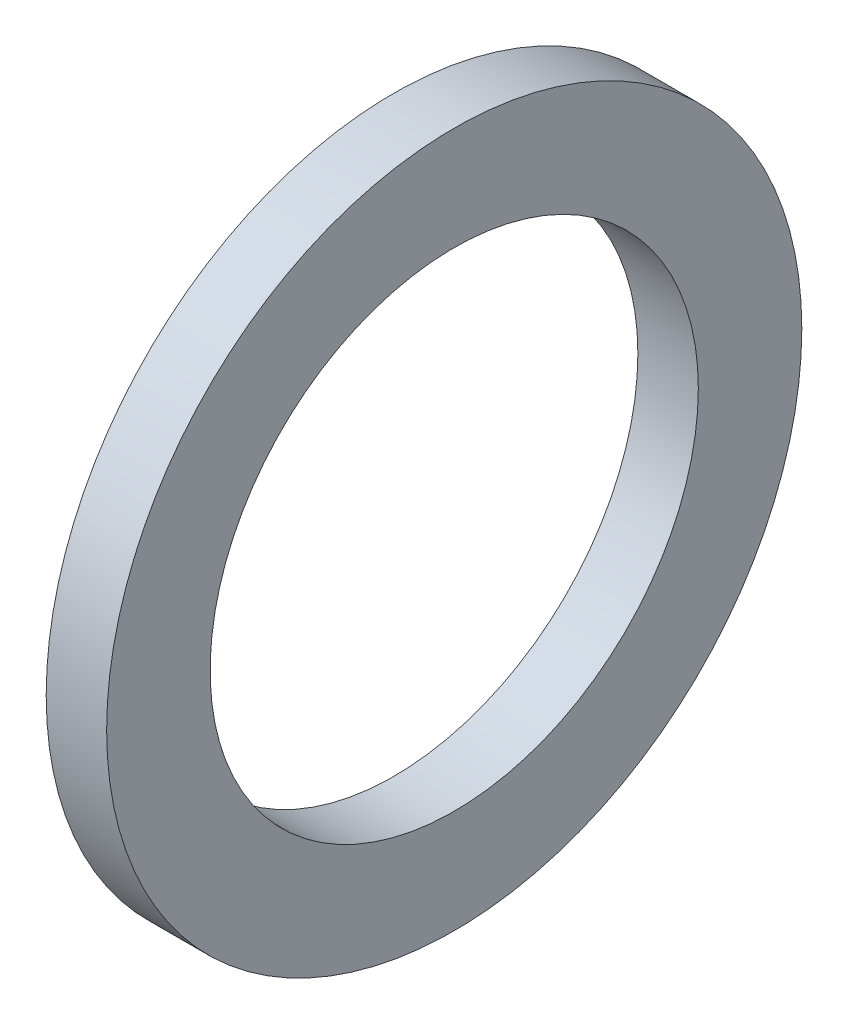
SolidWorks part; units mm, degrees
ref_plane "Front Plane" through (0, 0, 0) normal (0, 0, 1) x (1, 0, 0)
ref_plane "Top Plane" through (0, 0, 0) normal (0, 1, 0) x (1, 0, 0)
ref_plane "Right Plane" through (0, 0, 0) normal (1, 0, 0) x (0, 0, -1)
sketch "Sketch1" plane through (0, 0, 0) normal (1, 0, 0) x (0, 0, -1)
  circle A0 centre (0, 0) radius 11.5
  circle A1 centre (0, 0) radius 8.0761
  dimension "D1" = 23
  dimension "D2" = 16.1523
extrude "Boss-Extrude1" add sketch "Sketch1" along normal blind 2
